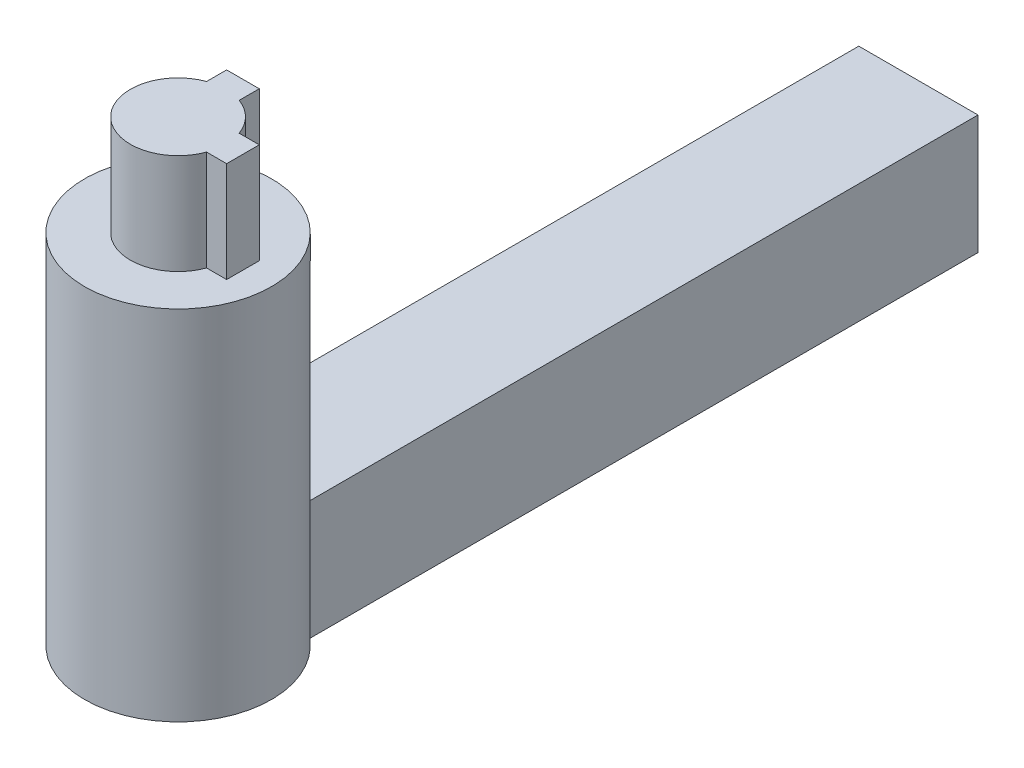
SolidWorks part; units mm, degrees
ref_plane "Front Plane" through (0, 0, 0) normal (0, 0, 1) x (1, 0, 0)
ref_plane "Top Plane" through (0, 0, 0) normal (0, 1, 0) x (1, 0, 0)
ref_plane "Right Plane" through (0, 0, 0) normal (1, 0, 0) x (0, 0, -1)
sketch "Sketch1" plane through (0, 0, 0) normal (0, 1, 0) x (1, 0, 0)
  line L1 (-4.75, 29.5) -> (4.75, 29.5)
  line L2 (-4.75, 29.5) -> (-4.75, -29.5)
  line L3 (-4.75, -29.5) -> (4.75, -29.5)
  line L4 (4.75, 29.5) -> (4.75, -29.5)
  line L5 (-4.75, 29.5) -> (4.75, -29.5) construction
  line L6 (-4.75, -29.5) -> (4.75, 29.5) construction
  point P0 (0, 0)
  dimension "D1" = 9.5
  dimension "D2" = 59
extrude "Boss-Extrude1" add sketch "Sketch1" along normal blind 9.5
sketch "Sketch2" plane through (0, 9.5, 0) normal (0, 1, 0) x (1, 0, 0)
  line L0 (-4.75, -29.5) -> (4.75, -29.5) construction
  circle A0 centre (0, -29.5) radius 7.45
  dimension "D1" = 14.9
extrude "Boss-Extrude2" add sketch "Sketch2" along normal blind 19 and the other way up to surface (9.5 mm away) other way up to face at (0, 0, 0)
sketch "Sketch3" plane through (0, 28.5, 0) normal (0, 1, 0) x (1, 0, 0)
  line L2 (-1.3, -25.9293) -> (-1.3, -24.3293)
  line L3 (-1.3, -24.3293) -> (1.3, -24.3293)
  line L4 (1.3, -25.9293) -> (1.3, -24.3293)
  line L5 (3.5707, -28.2) -> (5.1707, -28.2)
  line L7 (3.5707, -30.8) -> (5.1707, -30.8)
  line L8 (5.1707, -28.2) -> (5.1707, -30.8)
  arc A0 (-1.3, -25.9293) -> (3.5707, -30.8) centre (0, -29.5) ccw
  arc A1 (3.5707, -28.2) -> (1.3, -25.9293) centre (0, -29.5) ccw
  dimension "D1" = 7.6
  dimension "D2" = 2.6
  dimension "D3" = 1.6
  dimension "D4" = 2.6
  dimension "D5" = 1.6
  dimension "D6" = 1.6
  dimension "D7" = 1.6
extrude "Boss-Extrude3" add sketch "Sketch3" along normal blind 8
